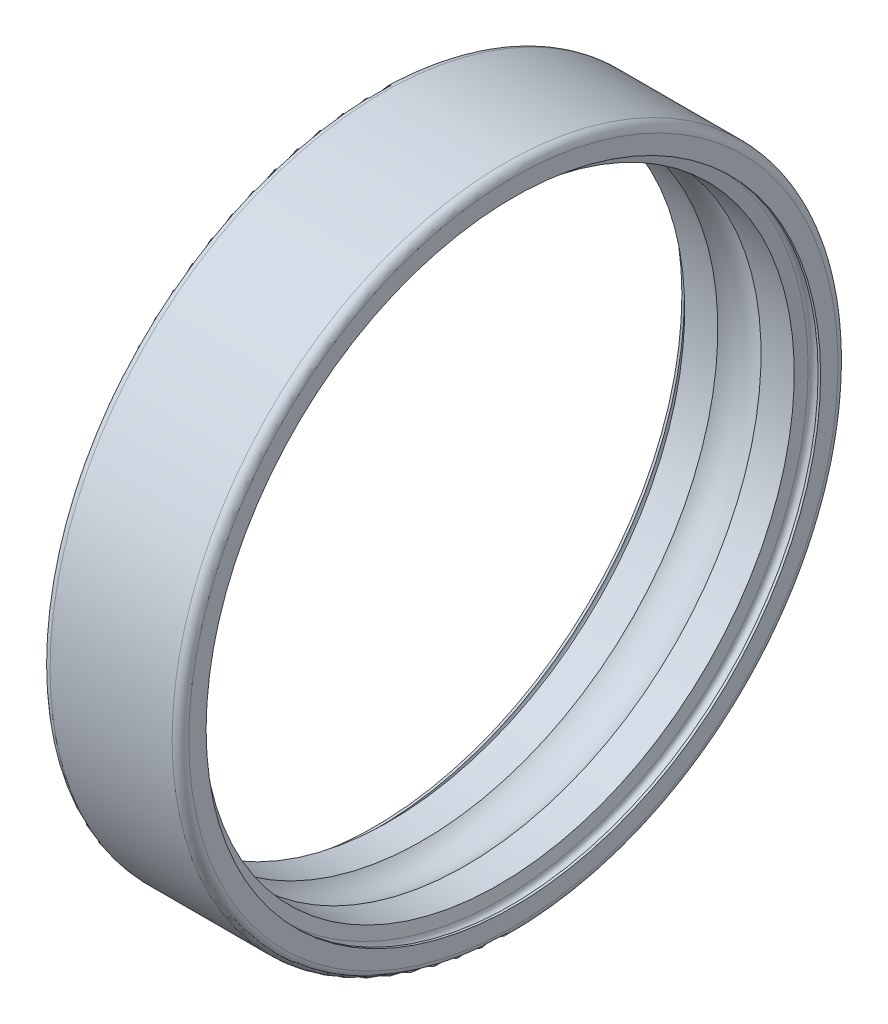
SolidWorks part; units mm, degrees
material "普通碳钢"
ref_plane "前视基准面" through (0, 0, 0) normal (0, 0, 1) x (1, 0, 0)
ref_plane "上视基准面" through (0, 0, 0) normal (0, 1, 0) x (1, 0, 0)
ref_plane "右视基准面" through (0, 0, 0) normal (1, 0, 0) x (0, 0, -1)
ref_plane "基准面1" through (0, 0, 0) normal (0, 0, 1) x (1, 0, 0)
sketch "草图1" plane through (0, 0, 0) normal (0, 0, 1) x (1, 0, 0)
  line L0 (0, 11.075) -> (0.09, 11.075)
  line L1 (0.45, 11.075) -> (0.5249, 10.65)
  line L2 (0.5249, 10.65) -> (1.7207, 10.65)
  line L3 (3.2793, 10.65) -> (4.4751, 10.65)
  line L4 (4.4751, 10.65) -> (4.55, 11.075)
  line L5 (4.91, 11.075) -> (5, 11.075)
  line L6 (5, 11.075) -> (5, 11.7)
  line L7 (4.7, 12) -> (0.3, 12)
  line L8 (0, 11.7) -> (0, 11.075)
  line L9 (50, 0) -> (-50, 0) construction
  arc A0 (0.09, 11.075) -> (0.45, 11.075) centre (0.27, 11.075) cw
  arc A1 (1.7207, 10.65) -> (3.2793, 10.65) centre (2.5, 9.75) cw
  arc A2 (4.55, 11.075) -> (4.91, 11.075) centre (4.73, 11.075) cw
  arc A3 (5, 11.7) -> (4.7, 12) centre (4.7, 11.7) ccw
  arc A4 (0.3, 12) -> (0, 11.7) centre (0.3, 11.7) ccw
revolve "旋转1" add sketch "草图1" angle 360 about L9
